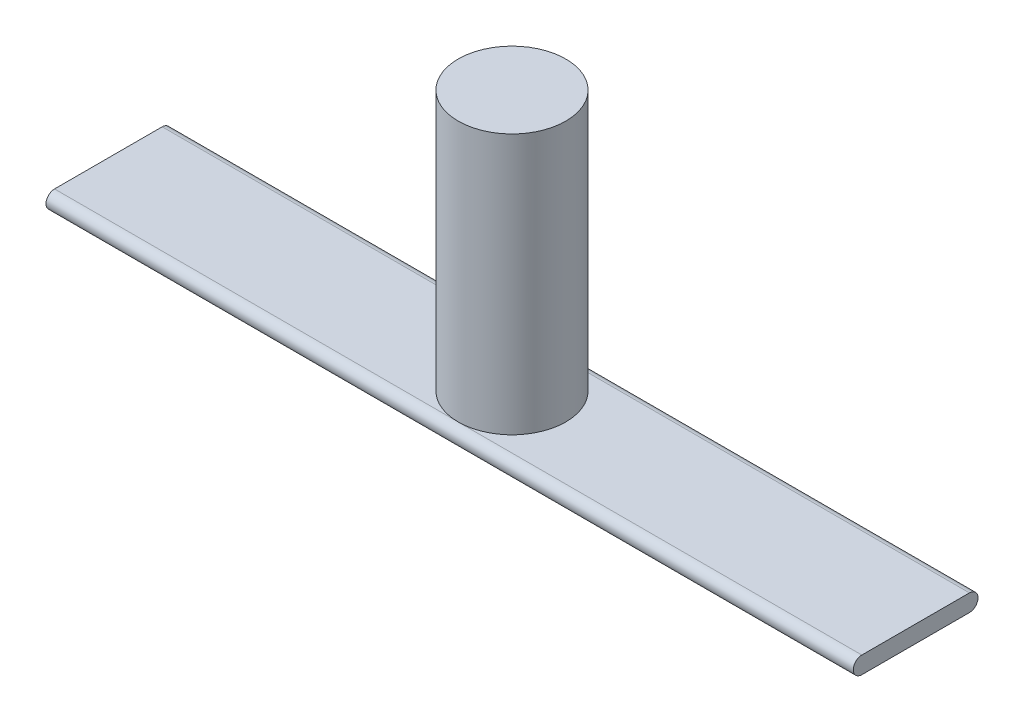
SolidWorks part; units mm, degrees
ref_plane "Front Plane" through (0, 0, 0) normal (0, 0, 1) x (1, 0, 0)
ref_plane "Top Plane" through (0, 0, 0) normal (0, 1, 0) x (1, 0, 0)
ref_plane "Right Plane" through (0, 0, 0) normal (1, 0, 0) x (0, 0, -1)
sketch "Sketch3" plane through (0, 0, 0) normal (0, 1, 0) x (1, 0, 0)
  circle A0 centre (0, 0) radius 1
  dimension "D1" = 2
extrude "Boss-Extrude1" add sketch "Sketch3" along normal blind 5
sketch "Sketch4" plane through (0, 0, 0) normal (1, 0, 0) x (0, 0, -1)
  line L0 (-1, 0) -> (1, 0) construction
  line L1 (-1, 0.1587) -> (1, 0.1587)
  line L2 (-1, -0.1587) -> (1, -0.1587)
  arc A0 (-1, 0.1587) -> (-1, -0.1587) centre (-1, 0) ccw
  arc A1 (1, -0.1587) -> (1, 0.1587) centre (1, 0) ccw
  point P2 (0, 0)
  dimension "D1" = 0.3173
  dimension "D2" = 2
extrude "Boss-Extrude2" add sketch "Sketch4" along normal mid plane 15
